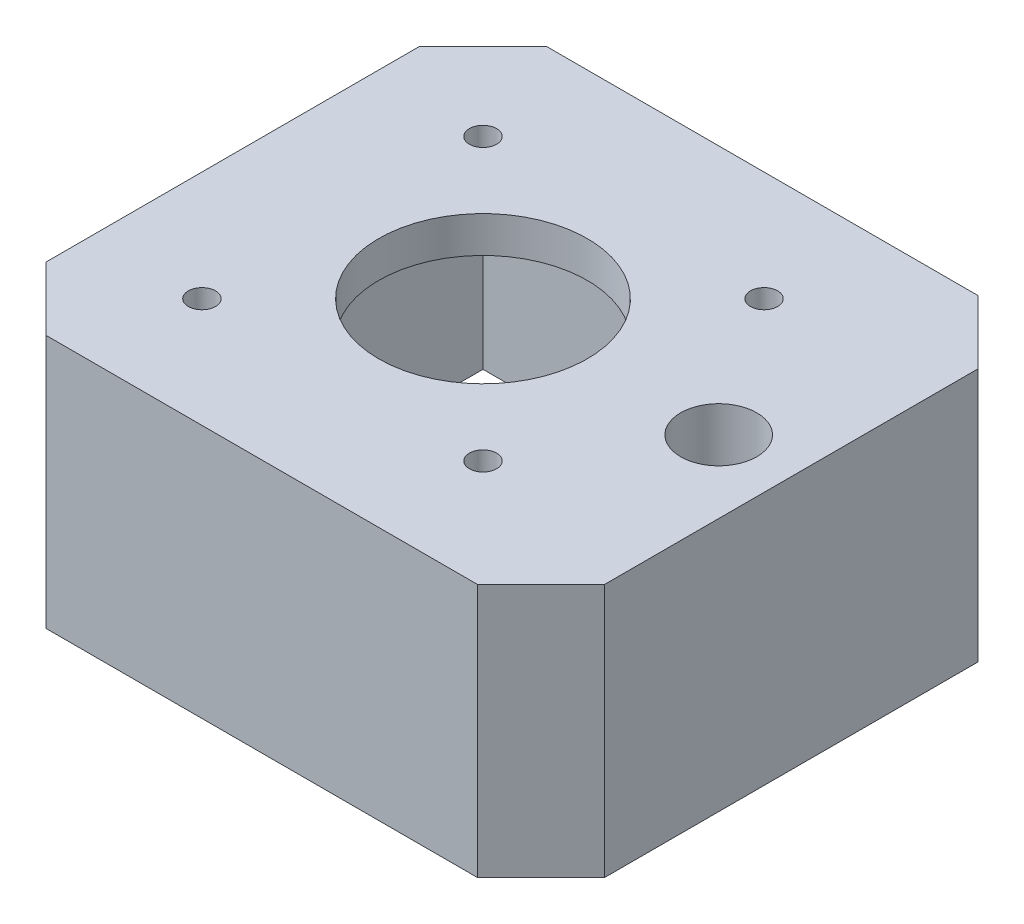
SolidWorks part; units mm, degrees
ref_plane "Front Plane" through (0, 0, 0) normal (0, 0, 1) x (1, 0, 0)
ref_plane "Top Plane" through (0, 0, 0) normal (0, 1, 0) x (1, 0, 0)
ref_plane "Right Plane" through (0, 0, 0) normal (1, 0, 0) x (0, 0, -1)
sketch "Sketch1" plane through (0, 0, 0) normal (0, 1, 0) x (1, 0, 0)
  line L0 (0, 21) -> (55, 21) construction
  line L1 (0, 0) -> (55, 0)
  line L2 (0, 0) -> (0, 42)
  line L3 (0, 42) -> (55, 42)
  line L4 (55, 0) -> (55, 42)
  line L5 (21, 42) -> (21, 0) construction
  circle A0 centre (47, 21) radius 4.2
  circle A1 centre (21, 21) radius 11.5
  circle A2 centre (5.5, 36.5) radius 1.5
  circle A3 centre (36.5, 36.5) radius 1.5
  circle A4 centre (5.5, 5.5) radius 1.5
  circle A5 centre (36.5, 5.5) radius 1.5
  point P8 (55, 21)
  dimension "D2" = 23
  dimension "D4" = 8.4
  dimension "D9" = 3
  dimension "D1" = 26
  dimension "D3" = 42
  dimension "D5" = 21
  dimension "D6" = 55
  dimension "D7" = 15.5
  dimension "D8" = 15.5
extrude "Boss-Extrude1" add sketch "Sketch1" along normal blind 4
sketch "Sketch2" plane through (0, 0, 0) normal (0, -1, 0) x (1, 0, 0)
  line L0 (0, 0) -> (55, 0) construction
  line L1 (40.4, 0) -> (42.25, 0)
  line L2 (40.4, 0) -> (40.4, -42)
  line L3 (40.4, -42) -> (42.25, -42)
  line L4 (42.25, 0) -> (42.25, -42)
  line L5 (55, -42) -> (0, -42) construction
  line L6 (55, 0) -> (55, -42) construction
  line L7 (55, -11) -> (42.25, -11)
  line L8 (55, -11) -> (55, -31)
  line L9 (55, -31) -> (42.25, -31)
  line L10 (42.25, -11) -> (42.25, -31)
  circle A0 centre (47, -21) radius 6.6
  circle A1 centre (47, -21) radius 4.2
  circle A2 centre (47, -21) radius 4.2 construction
  point P25 (55, -21)
  point P26 (55, -21)
  circle M7 centre (47, -21) radius 4.2
  line M10 (55, -42) -> (55, 0)
  dimension "D1" = 2.4
  dimension "D2" = 1.85
  dimension "D3" = 20
extrude "Boss-Extrude2" add sketch "Sketch2" along normal blind 20 contours L4 A0 L10 M7 | A0 L10 L9 L7 L4 M10
sketch "Sketch3" plane through (0, -20, 0) normal (0, -1, 0) x (1, 0, 0)
  line L1 (55, -31) -> (42.25, -31)
  line L2 (55, -31) -> (55, -11)
  line L3 (55, -11) -> (42.25, -11)
  line L4 (42.25, -31) -> (42.25, -11)
extrude "Boss-Extrude3" add sketch "Sketch3" along normal blind 4
sketch "Sketch4" plane through (0, 0, 0) normal (0, -1, 0) x (1, 0, 0)
  line L0 (42.25, -11) -> (42.25, -31) construction
  line L1 (42.25, 0.25) -> (-0.25, 0.25)
  line L2 (42.25, 0.25) -> (42.25, -42.25)
  line L3 (42.25, -42.25) -> (-0.25, -42.25)
  line L4 (-0.25, 0.25) -> (-0.25, -42.25)
  line L9 (48.6, 6.6) -> (-6.6, 6.6)
  line L10 (48.6, 6.6) -> (48.6, -48.6)
  line L11 (48.6, -48.6) -> (-6.6, -48.6)
  line L12 (-6.6, 6.6) -> (-6.6, -48.6)
  line L13 (55, -42) -> (0, -42) construction
  line L14 (0, -42) -> (0, 0) construction
  line L15 (0, 0) -> (55, 0) construction
  dimension "D1" = 0.25
  dimension "D2" = 0.25
  dimension "D3" = 0.25
  dimension "D4" = 6.35
  dimension "D5" = 6.35
  dimension "D6" = 6.35
  dimension "D7" = 6.35
extrude "Boss-Extrude4" add sketch "Sketch4" along normal up to surface (24 mm away) contours L10 L9 L12 L11 | L2 L1 L4 L3 up to face at (48.625, -24, -21)
sketch "Sketch5" plane through (0, 0, 0) normal (0, 1, 0) x (1, 0, 0)
  circle A0 centre (47, 21) radius 4.2
  circle A1 centre (47, 21) radius 4.2 construction
extrude "Cut-Extrude1" cut sketch "Sketch5" against normal up to surface (20 mm away) up to face at (49.9, -20, -21)
sketch "Sketch6" plane through (48.6, 0, 0) normal (1, 0, 0) x (0, 0, -1)
  line L0 (0, 4) -> (42, 4) construction
  line L1 (-6.6, 0) -> (0, 0)
  line L2 (-6.6, 0) -> (-6.6, 4)
  line L3 (-6.6, 4) -> (0, 4)
  line L4 (0, 0) -> (0, 4)
  line L5 (0, 4) -> (42, 4)
  line L6 (21, 4) -> (21, -2.4275) construction
  line L7 (48.6, 4) -> (42, 4)
  line L8 (42, 0) -> (42, 4)
  line L9 (48.6, 0) -> (42, 0)
  line L10 (48.6, 0) -> (48.6, 4)
  point P9 (21, 4)
  line M3 (0, 0) -> (-6.6, 0)
extrude "Boss-Extrude6" add sketch "Sketch6" against normal up to surface (48.6 mm away) contours L9 L10 L7 L8 | L4 L3 L2 M3 up to face at (0, 2, -21)
sketch "Sketch7" plane through (0, 0, -48.6) normal (0, 0, -1) x (-1, 0, 0)
  line L0 (6.6, -24) -> (6.6, 0) construction
  line L1 (0, 0) -> (6.6, 0)
  line L2 (0, 0) -> (0, 4)
  line L3 (0, 4) -> (6.6, 4)
  line L4 (6.6, 0) -> (6.6, 4)
extrude "Boss-Extrude7" add sketch "Sketch7" against normal up to surface (55.2 mm away) up to face at (14, -6.6667, 6.6)
sketch "Sketch8" plane through (48.6, 0, 0) normal (1, 0, 0) x (0, 0, -1)
  line L6 (42, 0) -> (31, 0)
  line L7 (31, 0) -> (31, -24)
  line L8 (31, -24) -> (48.6, -24)
  line L9 (48.6, -24) -> (48.6, 4)
  line L10 (48.6, 4) -> (42, 4)
  line L11 (42, 4) -> (42, 0)
  line L12 (42, 0) -> (31, 0)
  line L13 (31, 0) -> (31, -24)
  line L14 (31, -24) -> (48.6, -24)
  line L15 (48.6, -24) -> (48.6, 4)
  line L16 (48.6, 4) -> (42, 4)
  line L17 (42, 4) -> (42, 0)
  line L18 (11, -24) -> (11, 0)
  line L19 (11, 0) -> (0, 0)
  line L20 (0, 0) -> (0, 4)
  line L21 (0, 4) -> (-6.6, 4)
  line L22 (-6.6, 4) -> (-6.6, -24)
  line L23 (-6.6, -24) -> (11, -24)
  line L24 (11, -24) -> (11, 0)
  line L25 (11, 0) -> (0, 0)
  line L26 (0, 0) -> (0, 4)
  line L27 (0, 4) -> (-6.6, 4)
  line L28 (-6.6, 4) -> (-6.6, -24)
  line L29 (-6.6, -24) -> (11, -24)
  dimension "D1" = 0
  dimension "D2" = 0
extrude "Boss-Extrude8" add sketch "Sketch8" along normal up to surface (6.4 mm away) up to face at (55, -5, -21)
sketch "Sketch9" plane through (0, 4, 0) normal (0, 1, 0) x (1, 0, 0)
  line L0 (55, 0.4) -> (48, -6.6)
  line L1 (55, -6.6) -> (55, 48.6) construction
  line L2 (-6.6, -6.6) -> (55, -6.6) construction
  line L3 (48, -6.6) -> (55, -6.6)
  line L4 (55, -6.6) -> (55, 0.4)
  line L5 (55, 41.6) -> (48, 48.6)
  line L6 (-6.6, 48.6) -> (55, 48.6) construction
  line L7 (48, 48.6) -> (55, 48.6)
  line L8 (55, 48.6) -> (55, 41.6)
  line L9 (0.4, 48.6) -> (-6.6, 48.6)
  line L10 (-6.6, 48.6) -> (-6.6, 41.6)
  line L11 (-6.6, -6.6) -> (-6.6, 48.6) construction
  line L12 (-6.6, 41.6) -> (0.4, 48.6)
  line L13 (0.4, -6.6) -> (-6.6, 0.4)
  line L14 (-6.6, 0.4) -> (-6.6, -6.6)
  line L15 (-6.6, -6.6) -> (0.4, -6.6)
  dimension "D1" = 7
extrude "Cut-Extrude2" cut sketch "Sketch9" against normal up to surface (28 mm away)
equation "\"8mm hole\" = 8.4mm"
equation "\"22mm hole\"= 23mm"
equation "\"D2@Sketch1\"=\"22mm hole\""
equation "\"D4@Sketch1\"=\"8mm hole\""
